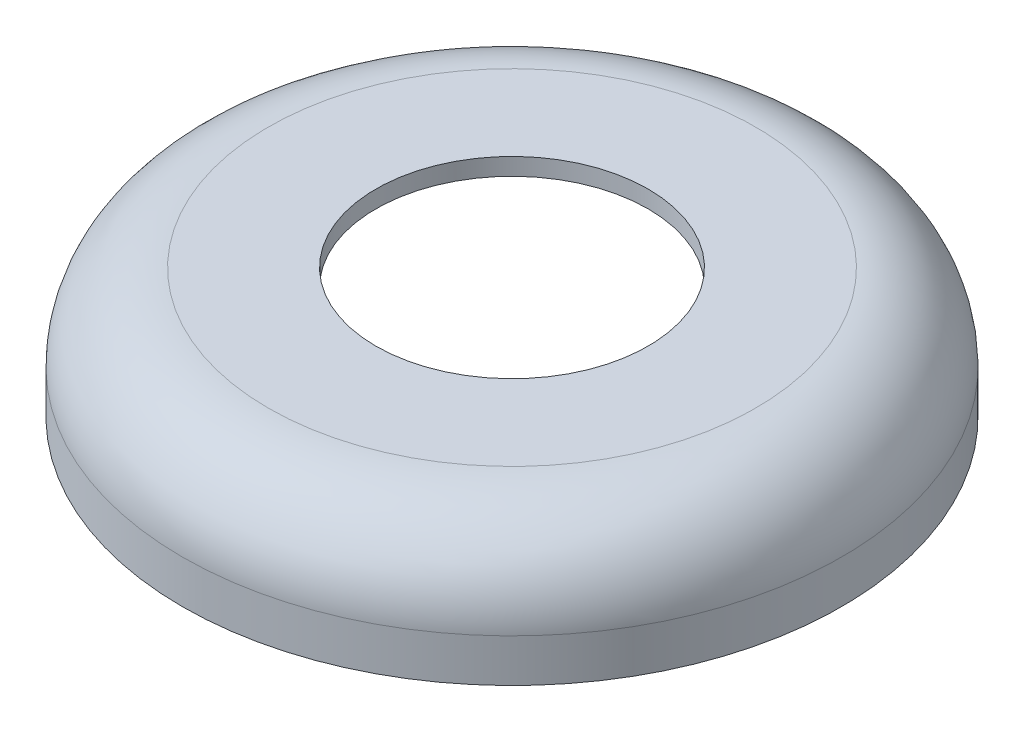
SolidWorks part; units mm, degrees
ref_plane "Front Plane" through (0, 0, 0) normal (0, 0, 1) x (1, 0, 0)
ref_plane "Top Plane" through (0, 0, 0) normal (0, 1, 0) x (1, 0, 0)
ref_plane "Right Plane" through (0, 0, 0) normal (1, 0, 0) x (0, 0, -1)
sketch "Sketch2" plane through (0, 0, 0) normal (0, 1, 0) x (1, 0, 0)
  circle A0 centre (0, 0) radius 11.5
extrude "Boss-Extrude1" add sketch "Sketch2" along normal blind 4.5
fillet "Fillet1" radius 3 1 edges at (0, 4.5, 11.5)
shell "Shell1" thickness 0.6
sketch "Sketch3" plane through (0, 4.5, 0) normal (0, 1, 0) x (1, 0, 0)
  circle A0 centre (0, 0) radius 4.75
extrude "Cut-Extrude1" cut sketch "Sketch3" against normal through all
